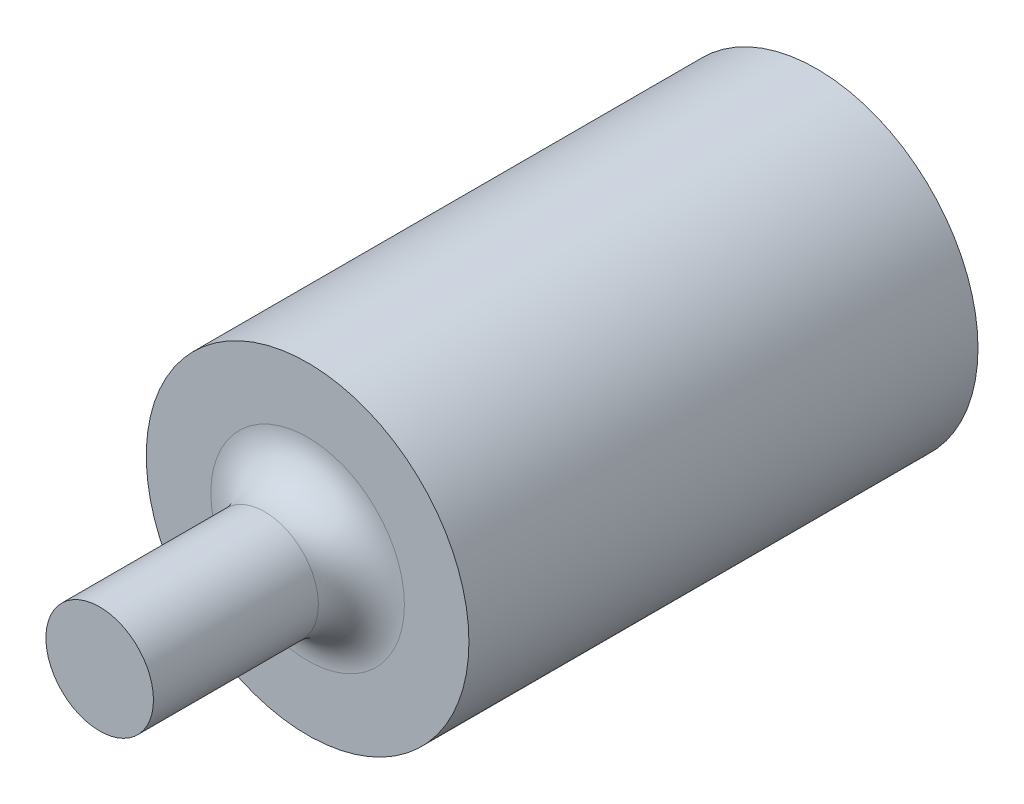
SolidWorks part; units mm, degrees
ref_plane "前基準面" through (0, 0, 0) normal (0, 0, 1) x (1, 0, 0)
ref_plane "上基準面" through (0, 0, 0) normal (0, 1, 0) x (1, 0, 0)
ref_plane "右基準面" through (0, 0, 0) normal (1, 0, 0) x (0, 0, -1)
sketch "草圖1" plane through (0, 0, 0) normal (0, 0, 1) x (1, 0, 0)
  circle A0 centre (0, 0) radius 11.25
  dimension "D1" = 22.5
extrude "填料-伸長1" add sketch "草圖1" along normal blind 35.5
sketch "草圖2" plane through (0, 0, 35.5) normal (0, 0, 1) x (1, 0, 0)
  circle A0 centre (0, 0) radius 3.75
  dimension "D1" = 7.5
extrude "填料-伸長2" add sketch "草圖2" along normal blind 14.5
fillet "圓角1" radius 3 1 edges at (3.75, 0, 35.5)
sketch "草圖3" plane through (0, 0, 0) normal (0, 0, -1) x (-1, 0, 0)
  circle A0 centre (-8.5, 0) radius 1.5
  circle A1 centre (8.5, 0) radius 1.5
  circle A2 centre (0, -8.5) radius 1.5
  circle A3 centre (0, 8.5) radius 1.5
extrude "除料-伸長1" cut sketch "草圖3" against normal blind 10
